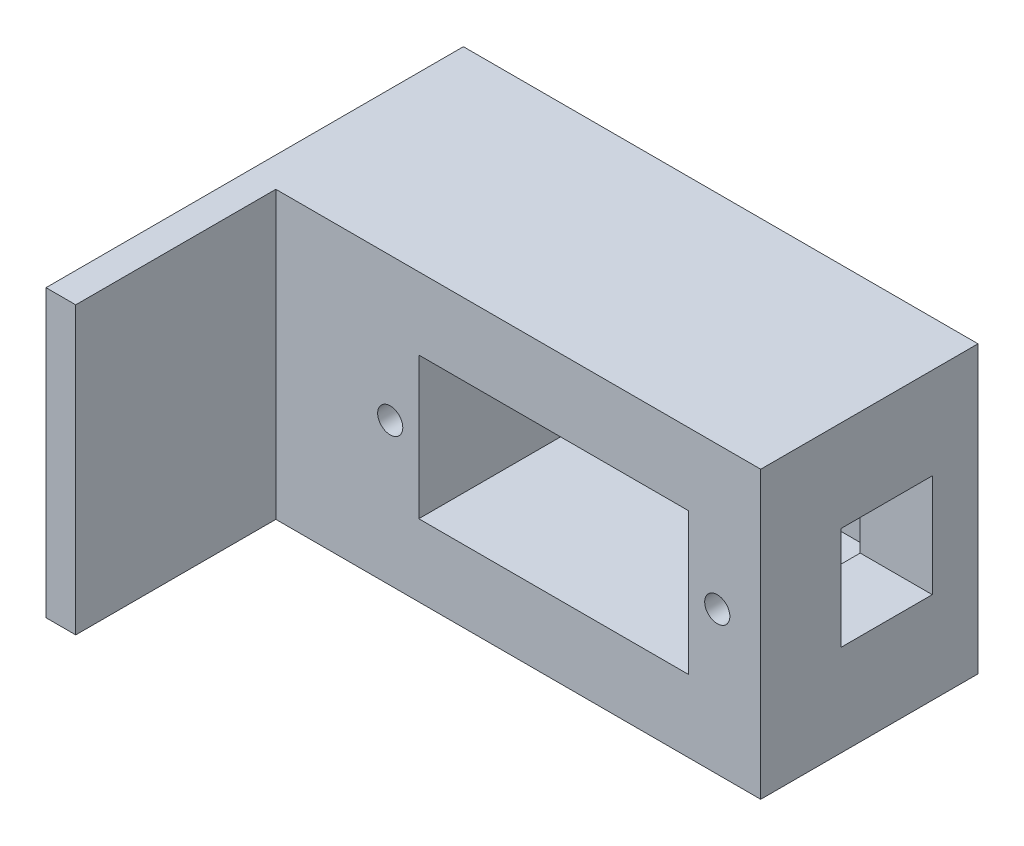
SolidWorks part; units mm, degrees
ref_plane "前基準面" through (0, 0, 0) normal (0, 0, 1) x (1, 0, 0)
ref_plane "上基準面" through (0, 0, 0) normal (0, 1, 0) x (1, 0, 0)
ref_plane "右基準面" through (0, 0, 0) normal (1, 0, 0) x (0, 0, -1)
sketch "草圖1" plane through (0, 0, 0) normal (0, 0, 1) x (1, 0, 0)
  line L5 (-65.029, 7.9036) -> (-20.029, 7.9036)
  line L6 (-65.029, 7.9036) -> (-65.029, -17.0964)
  line L7 (-65.029, -17.0964) -> (-20.029, -17.0964)
  line L8 (-20.029, 7.9036) -> (-20.029, -17.0964)
extrude "填料-伸長2" add sketch "草圖1" along normal blind 19 contours L6 L5 L8 L7
sketch "草圖4" plane through (0, 0, 19) normal (0, 0, 1) x (1, 0, 0)
  line L1 (-49.929, 1.6036) -> (-26.329, 1.6036)
  line L2 (-49.929, 1.6036) -> (-49.929, -10.7964)
  line L3 (-49.929, -10.7964) -> (-26.329, -10.7964)
  line L4 (-26.329, 1.6036) -> (-26.329, -10.7964)
  line L6 (-20.029, 7.9036) -> (-20.029, -17.0964) construction
  dimension "D1" = 6.3
extrude "除料-伸長2" cut sketch "草圖4" against normal blind 17.5
sketch "草圖5" plane through (-20.029, 0, 0) normal (1, 0, 0) x (0, 0, -1)
  line L0 (-19, 7.9036) -> (0, 7.9036) construction
  line L1 (-12, -0.0964) -> (-4, -0.0964)
  line L2 (-12, -0.0964) -> (-12, -9.0964)
  line L3 (-12, -9.0964) -> (-4, -9.0964)
  line L4 (-4, -0.0964) -> (-4, -9.0964)
  line L5 (0, 7.9036) -> (0, -17.0964) construction
  line L6 (-19, -17.0964) -> (0, -17.0964) construction
  dimension "D1" = 8
  dimension "D2" = 8
  dimension "D3" = 4
extrude "除料-伸長4" cut sketch "草圖5" against normal blind 7
sketch "草圖6" plane through (0, 0, 19) normal (0, 0, 1) x (1, 0, 0)
  line L0 (-65.029, 7.9036) -> (-20.029, 7.9036) construction
  line L1 (-26.329, -10.7964) -> (-26.329, 1.6036) construction
  line L2 (-49.929, 1.6036) -> (-49.929, -10.7964) construction
  circle A0 centre (-23.829, -4.5964) radius 1.1
  circle A1 centre (-52.429, -4.5964) radius 1.1
  point P2 (0, 0)
  dimension "D2" = 2.5
  dimension "D4" = 2.5
  dimension "D1" = 12.5
  dimension "D3" = 12.5
extrude "除料-伸長6" cut sketch "草圖6" against normal blind 7.5 contours A1 | A0
sketch "草圖8" plane through (0, 0, 19) normal (0, 0, 1) x (1, 0, 0)
  line L0 (-65.029, 7.9036) -> (-65.029, -17.0964) construction
  line L1 (-65.029, 7.9036) -> (-62.429, 7.9036)
  line L2 (-65.029, 7.9036) -> (-65.029, -17.0964)
  line L3 (-65.029, -17.0964) -> (-62.429, -17.0964)
  line L4 (-62.429, 7.9036) -> (-62.429, -17.0964)
  line L5 (-65.029, 7.9036) -> (-20.029, 7.9036) construction
  line L6 (-65.029, -17.0964) -> (-20.029, -17.0964) construction
extrude "填料-伸長3" add sketch "草圖8" along normal blind 17.5 contours L2 L1 L4 L3
